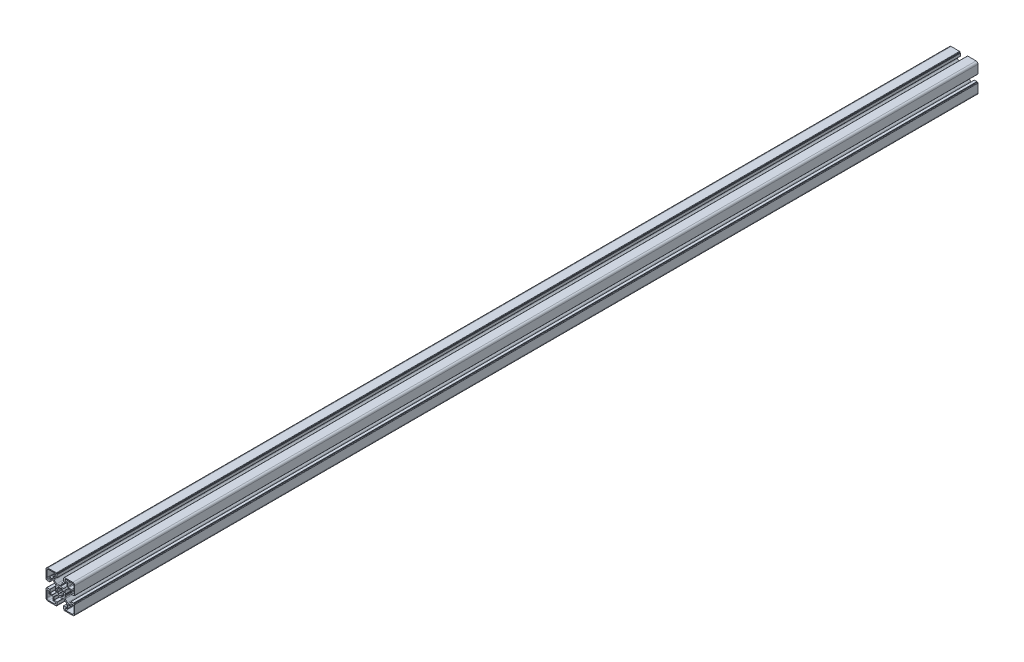
SolidWorks part; units mm, degrees
ref_plane "Plan de face" through (0, 0, 0) normal (0, 0, 1) x (1, 0, 0)
ref_plane "Plan de dessus" through (0, 0, 0) normal (0, 1, 0) x (1, 0, 0)
ref_plane "Plan de droite" through (0, 0, 0) normal (1, 0, 0) x (0, 0, -1)
sketch "Esquisse2" plane through (0, 0, 0) normal (0, 0, 1) x (1, 0, 0)
  line L28 (-195.0842, -352.0697) -> (-194.515, -352.1681)
  line L29 (-195.438, -354.39) -> (-195.9151, -354.0583)
  line L30 (-197.1408, -355.2803) -> (-196.8135, -355.7444)
  line L31 (-199.0372, -356.663) -> (-199.1374, -356.106)
  line L36 (-195.0842, -350.294) -> (-194.515, -350.1956)
  line L37 (-195.438, -347.9737) -> (-195.9151, -348.3053)
  line L38 (-197.1408, -347.0834) -> (-196.8135, -346.6192)
  line L39 (-199.0372, -345.7007) -> (-199.1374, -346.2577)
  line L40 (-200.9723, -356.663) -> (-200.8722, -356.106)
  line L41 (-202.8688, -355.2803) -> (-203.1961, -355.7444)
  line L42 (-204.5715, -354.39) -> (-204.0945, -354.0583)
  line L43 (-204.9253, -352.0697) -> (-205.4945, -352.1681)
  line L44 (-204.9253, -350.294) -> (-205.4945, -350.1956)
  line L45 (-204.5715, -347.9737) -> (-204.0945, -348.3053)
  line L46 (-202.8688, -347.0834) -> (-203.1961, -346.6192)
  line L47 (-200.9723, -345.7007) -> (-200.8722, -346.2577)
  line L105 (-200.0048, -338.2818) -> (-200.0048, -369.1677) construction
  line L107 (-190.0994, -351.1818) -> (-217.4619, -351.1818) construction
  line L108 (-191.0048, -330.1818) -> (-181.5048, -330.1818)
  line L109 (-189.4548, -333.1818) -> (-191.0048, -333.1818)
  line L116 (-221.0047, -332.6818) -> (-221.0047, -342.1816)
  line L117 (-218.0047, -342.1816) -> (-218.0047, -340.6318)
  line L118 (-217.0047, -339.6318) -> (-212.5547, -339.6318)
  line L119 (-211.5547, -338.6318) -> (-211.5547, -334.1818)
  line L120 (-210.5547, -333.1818) -> (-209.0047, -333.1818)
  line L121 (-209.0047, -330.1818) -> (-218.5047, -330.1818)
  line L122 (-188.4548, -338.6318) -> (-188.4548, -334.1818)
  line L123 (-183.0048, -339.6318) -> (-187.4548, -339.6318)
  line L124 (-182.0048, -342.1816) -> (-182.0048, -340.6318)
  line L125 (-179.0048, -332.6818) -> (-179.0048, -342.1816)
  line L126 (-191.0048, -372.1819) -> (-181.5048, -372.1819)
  line L127 (-189.4548, -369.1819) -> (-191.0048, -369.1819)
  line L128 (-188.4548, -363.7319) -> (-188.4548, -368.1819)
  line L129 (-183.0048, -362.7319) -> (-187.4548, -362.7319)
  line L130 (-182.0048, -360.182) -> (-182.0048, -361.7319)
  line L131 (-179.0048, -369.6819) -> (-179.0048, -360.182)
  line L196 (-192.4647, -351.135) -> (-192.0308, -350.3893)
  line L197 (-192.4413, -345.3231) -> (-188.875, -341.7569)
  line L198 (-187.5, -341.1873) -> (-183.6879, -341.1873)
  line L199 (-183.4879, -341.3873) -> (-183.4879, -345.9818)
  line L200 (-183.2879, -346.1818) -> (-179.2852, -346.1818)
  line L201 (-178.9852, -345.8818) -> (-178.9852, -345.6818)
  line L202 (-178.6852, -345.3818) -> (-178.0048, -345.3818)
  line L203 (-177.5048, -344.8818) -> (-177.5048, -331.6818)
  line L204 (-180.5048, -328.6818) -> (-193.6291, -328.6818)
  line L205 (-194.1291, -329.1818) -> (-194.1291, -329.8818)
  line L206 (-194.4291, -330.1818) -> (-194.7048, -330.1818)
  line L207 (-195.0048, -330.4818) -> (-195.0048, -334.515)
  line L208 (-194.8048, -334.715) -> (-190.0994, -334.715)
  line L209 (-189.8994, -334.915) -> (-189.8994, -338.7103)
  line L210 (-190.4852, -340.1245) -> (-194.0599, -343.6992)
  line L211 (-199.25, -343.207) -> (-199.8921, -343.5749)
  line L212 (-200.1174, -343.5749) -> (-200.7595, -343.207)
  line L213 (-205.9497, -343.6992) -> (-209.5244, -340.1245)
  line L214 (-210.1102, -338.7103) -> (-210.1102, -334.915)
  line L215 (-209.9102, -334.715) -> (-205.2048, -334.715)
  line L216 (-205.0048, -334.515) -> (-205.0048, -330.4818)
  line L217 (-205.3048, -330.1818) -> (-205.5805, -330.1818)
  line L218 (-205.8805, -329.8818) -> (-205.8805, -329.1818)
  line L219 (-206.3805, -328.6818) -> (-219.5047, -328.6818)
  line L220 (-222.5047, -331.6818) -> (-222.5047, -344.8818)
  line L221 (-222.0047, -345.3818) -> (-221.3244, -345.3818)
  line L222 (-221.0244, -345.6818) -> (-221.0244, -345.8818)
  line L223 (-220.7244, -346.1818) -> (-216.7217, -346.1818)
  line L224 (-216.5217, -345.9818) -> (-216.5217, -341.3873)
  line L225 (-216.3217, -341.1873) -> (-212.5095, -341.1873)
  line L226 (-211.1345, -341.7569) -> (-207.5682, -345.3231)
  line L227 (-207.9787, -350.3893) -> (-207.5448, -351.135)
  line L228 (-207.5448, -351.2287) -> (-207.9787, -351.9744)
  line L229 (-207.5682, -357.0405) -> (-211.1345, -360.6068)
  line L230 (-212.5095, -361.1764) -> (-216.3217, -361.1764)
  line L231 (-216.5217, -360.9764) -> (-216.5217, -356.3819)
  line L232 (-216.7217, -356.1819) -> (-220.7244, -356.1819)
  line L233 (-221.0244, -356.4819) -> (-221.0244, -356.6818)
  line L234 (-221.3244, -356.9818) -> (-222.0047, -356.9818)
  line L235 (-222.5047, -357.4818) -> (-222.5047, -370.6819)
  line L236 (-219.5047, -373.6819) -> (-206.3805, -373.6819)
  line L237 (-205.8805, -373.1819) -> (-205.8805, -372.4819)
  line L238 (-205.5805, -372.1819) -> (-205.3048, -372.1819)
  line L239 (-205.0048, -371.8819) -> (-205.0048, -367.8487)
  line L240 (-205.2048, -367.6487) -> (-209.9102, -367.6487)
  line L241 (-210.1102, -367.4487) -> (-210.1102, -363.6534)
  line L242 (-209.5244, -362.2392) -> (-205.9497, -358.6645)
  line L243 (-200.7595, -359.1566) -> (-200.1174, -358.7888)
  line L244 (-199.8921, -358.7888) -> (-199.25, -359.1566)
  line L245 (-194.0599, -358.6645) -> (-190.4852, -362.2392)
  line L246 (-189.8994, -363.6534) -> (-189.8994, -367.4487)
  line L247 (-190.0994, -367.6487) -> (-194.8048, -367.6487)
  line L248 (-195.0048, -367.8487) -> (-195.0048, -371.8819)
  line L249 (-194.7048, -372.1819) -> (-194.4291, -372.1819)
  line L250 (-194.1291, -372.4819) -> (-194.1291, -373.1819)
  line L251 (-193.6291, -373.6819) -> (-180.5048, -373.6819)
  line L252 (-177.5048, -370.6819) -> (-177.5048, -357.4818)
  line L253 (-178.0048, -356.9818) -> (-178.6852, -356.9818)
  line L254 (-178.9852, -356.6818) -> (-178.9852, -356.4819)
  line L255 (-179.2852, -356.1819) -> (-183.2879, -356.1819)
  line L256 (-183.4879, -356.3819) -> (-183.4879, -360.9764)
  line L257 (-183.6879, -361.1764) -> (-187.5, -361.1764)
  line L258 (-188.875, -360.6068) -> (-192.4413, -357.0405)
  line L259 (-192.0308, -351.9744) -> (-192.4647, -351.2287)
  line L260 (-209.0047, -372.1819) -> (-218.5047, -372.1819)
  line L261 (-210.5547, -369.1819) -> (-209.0047, -369.1819)
  line L262 (-211.5547, -363.7319) -> (-211.5547, -368.1819)
  line L263 (-217.0047, -362.7319) -> (-212.5547, -362.7319)
  line L264 (-218.0047, -360.182) -> (-218.0047, -361.7319)
  line L265 (-221.0047, -369.6819) -> (-221.0047, -360.182)
  arc A63 (-194.515, -352.1681) -> (-194.0979, -352.793) centre (-194.5809, -352.6637) cw
  arc A64 (-194.0979, -352.793) -> (-194.7023, -354.2383) centre (-199.9813, -351.1818) cw
  arc A65 (-194.7023, -354.2383) -> (-195.438, -354.39) centre (-195.1368, -353.9909) cw
  arc A66 (-195.9151, -354.0583) -> (-197.1408, -355.2803) centre (-200.0048, -351.1818) cw
  arc A67 (-196.8135, -355.7444) -> (-196.9604, -356.4813) centre (-197.2105, -356.0483) cw
  arc A68 (-196.9604, -356.4813) -> (-198.4097, -357.0759) centre (-199.9813, -351.1818) cw
  arc A69 (-198.4097, -357.0759) -> (-199.0372, -356.663) centre (-198.5421, -356.5938) cw
  arc A70 (-199.1374, -356.106) -> (-200.8722, -356.106) centre (-200.0048, -351.1818) cw
  arc A71 (-201.5998, -357.0759) -> (-200.9723, -356.663) centre (-201.4675, -356.5938) ccw
  arc A81 (-195.0842, -352.0697) -> (-195.0842, -350.294) centre (-200.0048, -351.1818) ccw
  arc A82 (-194.515, -350.1956) -> (-194.0979, -349.5706) centre (-194.5809, -349.7) ccw
  arc A83 (-194.0979, -349.5706) -> (-194.7023, -348.1254) centre (-199.9813, -351.1818) ccw
  arc A84 (-194.7023, -348.1254) -> (-195.438, -347.9737) centre (-195.1368, -348.3728) ccw
  arc A85 (-195.9151, -348.3053) -> (-197.1408, -347.0834) centre (-200.0048, -351.1818) ccw
  arc A86 (-196.8135, -346.6192) -> (-196.9604, -345.8824) centre (-197.2105, -346.3153) ccw
  arc A87 (-196.9604, -345.8824) -> (-198.4097, -345.2878) centre (-199.9813, -351.1818) ccw
  arc A88 (-198.4097, -345.2878) -> (-199.0372, -345.7007) centre (-198.5421, -345.7699) ccw
  arc A89 (-199.1374, -346.2577) -> (-200.8722, -346.2577) centre (-200.0048, -351.1818) ccw
  arc A90 (-203.0492, -356.4813) -> (-201.5998, -357.0759) centre (-200.0282, -351.1818) ccw
  arc A91 (-203.1961, -355.7444) -> (-203.0492, -356.4813) centre (-202.799, -356.0483) ccw
  arc A92 (-204.0945, -354.0583) -> (-202.8688, -355.2803) centre (-200.0048, -351.1818) ccw
  arc A93 (-205.3073, -354.2383) -> (-204.5715, -354.39) centre (-204.8728, -353.9909) ccw
  arc A94 (-205.9116, -352.793) -> (-205.3073, -354.2383) centre (-200.0282, -351.1818) ccw
  arc A95 (-205.4945, -352.1681) -> (-205.9116, -352.793) centre (-205.4286, -352.6637) ccw
  arc A96 (-204.9253, -352.0697) -> (-204.9253, -350.294) centre (-200.0048, -351.1818) cw
  arc A97 (-205.4945, -350.1956) -> (-205.9116, -349.5706) centre (-205.4286, -349.7) cw
  arc A98 (-205.9116, -349.5706) -> (-205.3073, -348.1254) centre (-200.0282, -351.1818) cw
  arc A99 (-205.3073, -348.1254) -> (-204.5715, -347.9737) centre (-204.8728, -348.3728) cw
  arc A100 (-204.0945, -348.3053) -> (-202.8688, -347.0834) centre (-200.0048, -351.1818) cw
  arc A101 (-203.1961, -346.6192) -> (-203.0492, -345.8824) centre (-202.799, -346.3153) cw
  arc A102 (-203.0492, -345.8824) -> (-201.5998, -345.2878) centre (-200.0282, -351.1818) cw
  arc A103 (-201.5998, -345.2878) -> (-200.9723, -345.7007) centre (-201.4675, -345.7699) cw
  arc A128 (-181.5048, -330.1818) -> (-179.0048, -332.6818) centre (-181.5048, -332.6818) cw
  arc A129 (-191.0048, -333.1818) -> (-191.0048, -330.1818) centre (-191.0048, -331.6818) cw
  arc A130 (-189.4548, -333.1818) -> (-188.4548, -334.1818) centre (-189.4548, -334.1818) cw
  arc A131 (-187.4548, -339.6318) -> (-188.4548, -338.6318) centre (-187.4548, -338.6318) cw
  arc A132 (-183.0048, -339.6318) -> (-182.0048, -340.6318) centre (-183.0048, -340.6318) cw
  arc A133 (-179.0048, -342.1816) -> (-182.0048, -342.1816) centre (-180.5048, -342.1816) cw
  arc A140 (-221.0047, -342.1816) -> (-218.0047, -342.1816) centre (-219.5047, -342.1816) ccw
  arc A141 (-217.0047, -339.6318) -> (-218.0047, -340.6318) centre (-217.0047, -340.6318) ccw
  arc A142 (-212.5547, -339.6318) -> (-211.5547, -338.6318) centre (-212.5547, -338.6318) ccw
  arc A143 (-210.5547, -333.1818) -> (-211.5547, -334.1818) centre (-210.5547, -334.1818) ccw
  arc A144 (-209.0047, -333.1818) -> (-209.0047, -330.1818) centre (-209.0047, -331.6818) ccw
  arc A145 (-218.5047, -330.1818) -> (-221.0047, -332.6818) centre (-218.5047, -332.6818) ccw
  arc A146 (-191.0048, -369.1819) -> (-191.0048, -372.1819) centre (-191.0048, -370.6819) ccw
  arc A147 (-189.4548, -369.1819) -> (-188.4548, -368.1819) centre (-189.4548, -368.1819) ccw
  arc A148 (-187.4548, -362.7319) -> (-188.4548, -363.7319) centre (-187.4548, -363.7319) ccw
  arc A149 (-183.0048, -362.7319) -> (-182.0048, -361.7319) centre (-183.0048, -361.7319) ccw
  arc A150 (-179.0048, -360.182) -> (-182.0048, -360.182) centre (-180.5048, -360.182) ccw
  arc A151 (-181.5048, -372.1819) -> (-179.0048, -369.6819) centre (-181.5048, -369.6819) ccw
  arc A152 (-218.5047, -372.1819) -> (-221.0047, -369.6819) centre (-218.5047, -369.6819) cw
  arc A153 (-209.0047, -369.1819) -> (-209.0047, -372.1819) centre (-209.0047, -370.6819) cw
  arc A154 (-210.5547, -369.1819) -> (-211.5547, -368.1819) centre (-210.5547, -368.1819) cw
  arc A155 (-212.5547, -362.7319) -> (-211.5547, -363.7319) centre (-212.5547, -363.7319) cw
  arc A156 (-217.0047, -362.7319) -> (-218.0047, -361.7319) centre (-217.0047, -361.7319) cw
  arc A157 (-221.0047, -360.182) -> (-218.0047, -360.182) centre (-219.5047, -360.182) cw
  arc A254 (-192.4647, -351.135) -> (-192.4734, -351.1818) centre (-192.2739, -351.1948) ccw
  arc A255 (-192.0308, -350.3893) -> (-192.0048, -350.2678) centre (-192.2037, -350.2887) ccw
  arc A256 (-192.0048, -350.2678) -> (-192.8044, -347.57) centre (-199.9552, -351.157) ccw
  arc A257 (-192.4413, -345.3231) -> (-192.8044, -347.57) centre (-191.0663, -346.6981) ccw
  arc A258 (-187.5, -341.1873) -> (-188.875, -341.7569) centre (-187.5, -343.1318) ccw
  arc A259 (-183.4879, -341.3873) -> (-183.6879, -341.1873) centre (-183.6879, -341.3873) ccw
  arc A260 (-183.4879, -345.9818) -> (-183.2879, -346.1818) centre (-183.2879, -345.9818) ccw
  arc A261 (-179.2852, -346.1818) -> (-178.9852, -345.8818) centre (-179.2852, -345.8818) ccw
  arc A262 (-178.6852, -345.3818) -> (-178.9852, -345.6818) centre (-178.6852, -345.6818) ccw
  arc A263 (-178.0048, -345.3818) -> (-177.5048, -344.8818) centre (-178.0048, -344.8818) ccw
  arc A264 (-177.5048, -331.6818) -> (-180.5048, -328.6818) centre (-180.5048, -331.6818) ccw
  arc A265 (-193.6291, -328.6818) -> (-194.1291, -329.1818) centre (-193.6291, -329.1818) ccw
  arc A266 (-194.4291, -330.1818) -> (-194.1291, -329.8818) centre (-194.4291, -329.8818) ccw
  arc A267 (-194.7048, -330.1818) -> (-195.0048, -330.4818) centre (-194.7048, -330.4818) ccw
  arc A268 (-195.0048, -334.515) -> (-194.8048, -334.715) centre (-194.8048, -334.515) ccw
  arc A269 (-189.8994, -334.915) -> (-190.0994, -334.715) centre (-190.0994, -334.915) ccw
  arc A270 (-190.4852, -340.1245) -> (-189.8994, -338.7103) centre (-191.8994, -338.7103) ccw
  arc A271 (-196.3383, -344.0086) -> (-194.0599, -343.6992) centre (-195.4193, -342.2322) ccw
  arc A272 (-196.3383, -344.0086) -> (-199.1284, -343.1818) centre (-199.9813, -351.1818) ccw
  arc A273 (-199.1284, -343.1818) -> (-199.25, -343.207) centre (-199.1506, -343.3806) ccw
  arc A274 (-200.0048, -343.6509) -> (-199.8921, -343.5749) centre (-200.0537, -343.457) ccw
  arc A275 (-200.1174, -343.5749) -> (-200.0048, -343.6509) centre (-199.9559, -343.457) ccw
  arc A276 (-200.7595, -343.207) -> (-200.8812, -343.1818) centre (-200.8589, -343.3806) ccw
  arc A277 (-200.8812, -343.1818) -> (-203.6713, -344.0086) centre (-200.0282, -351.1818) ccw
  arc A278 (-205.9497, -343.6992) -> (-203.6713, -344.0086) centre (-204.5903, -342.2322) ccw
  arc A279 (-210.1102, -338.7103) -> (-209.5244, -340.1245) centre (-208.1102, -338.7103) ccw
  arc A280 (-209.9102, -334.715) -> (-210.1102, -334.915) centre (-209.9102, -334.915) ccw
  arc A281 (-205.2048, -334.715) -> (-205.0048, -334.515) centre (-205.2048, -334.515) ccw
  arc A282 (-205.0048, -330.4818) -> (-205.3048, -330.1818) centre (-205.3048, -330.4818) ccw
  arc A283 (-205.8805, -329.8818) -> (-205.5805, -330.1818) centre (-205.5805, -329.8818) ccw
  arc A284 (-205.8805, -329.1818) -> (-206.3805, -328.6818) centre (-206.3805, -329.1818) ccw
  arc A285 (-219.5047, -328.6818) -> (-222.5047, -331.6818) centre (-219.5047, -331.6818) ccw
  arc A286 (-222.5047, -344.8818) -> (-222.0047, -345.3818) centre (-222.0047, -344.8818) ccw
  arc A287 (-221.0244, -345.6818) -> (-221.3244, -345.3818) centre (-221.3244, -345.6818) ccw
  arc A288 (-221.0244, -345.8818) -> (-220.7244, -346.1818) centre (-220.7244, -345.8818) ccw
  arc A289 (-216.7217, -346.1818) -> (-216.5217, -345.9818) centre (-216.7217, -345.9818) ccw
  arc A290 (-216.3217, -341.1873) -> (-216.5217, -341.3873) centre (-216.3217, -341.3873) ccw
  arc A291 (-211.1345, -341.7569) -> (-212.5095, -341.1873) centre (-212.5095, -343.1318) ccw
  arc A292 (-207.2051, -347.57) -> (-207.5682, -345.3231) centre (-208.9432, -346.6981) ccw
  arc A293 (-207.2051, -347.57) -> (-208.0048, -350.2678) centre (-200.0543, -351.157) ccw
  arc A294 (-208.0048, -350.2678) -> (-207.9787, -350.3893) centre (-207.8059, -350.2887) ccw
  arc A295 (-207.5361, -351.1818) -> (-207.5448, -351.135) centre (-207.7357, -351.1948) ccw
  arc A296 (-207.5448, -351.2287) -> (-207.5361, -351.1818) centre (-207.7357, -351.1689) ccw
  arc A297 (-207.9787, -351.9744) -> (-208.0048, -352.0959) centre (-207.8059, -352.075) ccw
  arc A298 (-208.0048, -352.0959) -> (-207.2051, -354.7937) centre (-200.0543, -351.2067) ccw
  arc A299 (-207.5682, -357.0405) -> (-207.2051, -354.7937) centre (-208.9432, -355.6656) ccw
  arc A300 (-212.5095, -361.1764) -> (-211.1345, -360.6068) centre (-212.5095, -359.2319) ccw
  arc A301 (-216.5217, -360.9764) -> (-216.3217, -361.1764) centre (-216.3217, -360.9764) ccw
  arc A302 (-216.5217, -356.3819) -> (-216.7217, -356.1819) centre (-216.7217, -356.3819) ccw
  arc A303 (-220.7244, -356.1819) -> (-221.0244, -356.4819) centre (-220.7244, -356.4819) ccw
  arc A304 (-221.3244, -356.9818) -> (-221.0244, -356.6818) centre (-221.3244, -356.6818) ccw
  arc A305 (-222.0047, -356.9818) -> (-222.5047, -357.4818) centre (-222.0047, -357.4818) ccw
  arc A306 (-222.5047, -370.6819) -> (-219.5047, -373.6819) centre (-219.5047, -370.6819) ccw
  arc A307 (-206.3805, -373.6819) -> (-205.8805, -373.1819) centre (-206.3805, -373.1819) ccw
  arc A308 (-205.5805, -372.1819) -> (-205.8805, -372.4819) centre (-205.5805, -372.4819) ccw
  arc A309 (-205.3048, -372.1819) -> (-205.0048, -371.8819) centre (-205.3048, -371.8819) ccw
  arc A310 (-205.0048, -367.8487) -> (-205.2048, -367.6487) centre (-205.2048, -367.8487) ccw
  arc A311 (-210.1102, -367.4487) -> (-209.9102, -367.6487) centre (-209.9102, -367.4487) ccw
  arc A312 (-209.5244, -362.2392) -> (-210.1102, -363.6534) centre (-208.1102, -363.6534) ccw
  arc A313 (-203.6713, -358.3551) -> (-205.9497, -358.6645) centre (-204.5903, -360.1315) ccw
  arc A314 (-203.6713, -358.3551) -> (-200.8812, -359.1819) centre (-200.0282, -351.1818) ccw
  arc A315 (-200.8812, -359.1819) -> (-200.7595, -359.1566) centre (-200.8589, -358.9831) ccw
  arc A316 (-200.0048, -358.7128) -> (-200.1174, -358.7888) centre (-199.9559, -358.9067) ccw
  arc A317 (-199.8921, -358.7888) -> (-200.0048, -358.7128) centre (-200.0537, -358.9067) ccw
  arc A318 (-199.25, -359.1566) -> (-199.1284, -359.1819) centre (-199.1506, -358.9831) ccw
  arc A319 (-199.1284, -359.1819) -> (-196.3383, -358.3551) centre (-199.9813, -351.1818) ccw
  arc A320 (-194.0599, -358.6645) -> (-196.3383, -358.3551) centre (-195.4193, -360.1315) ccw
  arc A321 (-189.8994, -363.6534) -> (-190.4852, -362.2392) centre (-191.8994, -363.6534) ccw
  arc A322 (-190.0994, -367.6487) -> (-189.8994, -367.4487) centre (-190.0994, -367.4487) ccw
  arc A323 (-194.8048, -367.6487) -> (-195.0048, -367.8487) centre (-194.8048, -367.8487) ccw
  arc A324 (-195.0048, -371.8819) -> (-194.7048, -372.1819) centre (-194.7048, -371.8819) ccw
  arc A325 (-194.1291, -372.4819) -> (-194.4291, -372.1819) centre (-194.4291, -372.4819) ccw
  arc A326 (-194.1291, -373.1819) -> (-193.6291, -373.6819) centre (-193.6291, -373.1819) ccw
  arc A327 (-180.5048, -373.6819) -> (-177.5048, -370.6819) centre (-180.5048, -370.6819) ccw
  arc A328 (-177.5048, -357.4818) -> (-178.0048, -356.9818) centre (-178.0048, -357.4818) ccw
  arc A329 (-178.9852, -356.6818) -> (-178.6852, -356.9818) centre (-178.6852, -356.6818) ccw
  arc A330 (-178.9852, -356.4819) -> (-179.2852, -356.1819) centre (-179.2852, -356.4819) ccw
  arc A331 (-183.2879, -356.1819) -> (-183.4879, -356.3819) centre (-183.2879, -356.3819) ccw
  arc A332 (-183.6879, -361.1764) -> (-183.4879, -360.9764) centre (-183.6879, -360.9764) ccw
  arc A333 (-188.875, -360.6068) -> (-187.5, -361.1764) centre (-187.5, -359.2319) ccw
  arc A334 (-192.8044, -354.7937) -> (-192.4413, -357.0405) centre (-191.0663, -355.6656) ccw
  arc A335 (-192.8044, -354.7937) -> (-192.0048, -352.0959) centre (-199.9552, -351.2067) ccw
  arc A336 (-192.0048, -352.0959) -> (-192.0308, -351.9744) centre (-192.2037, -352.075) ccw
  arc A337 (-192.4734, -351.1818) -> (-192.4647, -351.2287) centre (-192.2739, -351.1689) ccw
extrude "Boss.-Extru.1" add sketch "Esquisse2" along normal blind 1415
